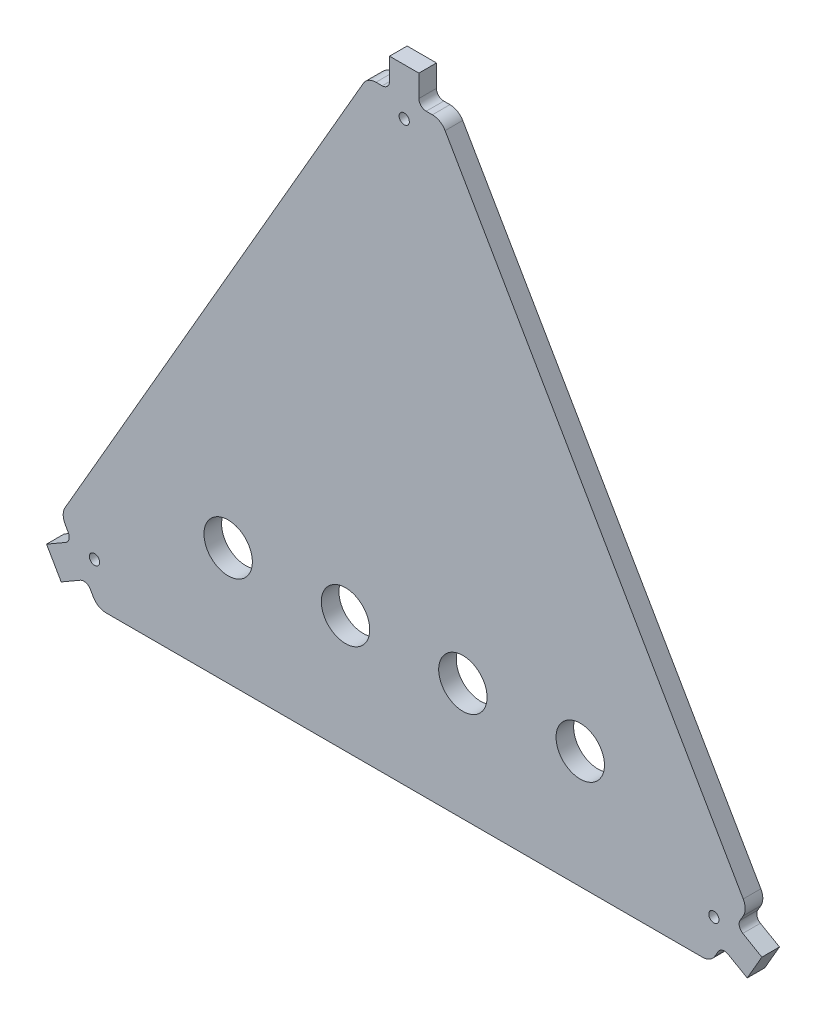
SolidWorks part; units mm, degrees
material "Pine"
ref_plane "Front Plane" through (0, 0, 0) normal (0, 0, 1) x (1, 0, 0)
ref_plane "Top Plane" through (0, 0, 0) normal (0, 1, 0) x (1, 0, 0)
ref_plane "Right Plane" through (0, 0, 0) normal (1, 0, 0) x (0, 0, -1)
sketch "Sketch1" plane through (0, 0, 0) normal (0, 0, 1) x (1, 0, 0)
  line L0 (-209, 0) -> (209, 0)
  line L1 (209, 0) -> (234, 43.3013)
  line L2 (234, 43.3013) -> (25, 405.2999)
  line L3 (25, 405.2999) -> (-25, 405.2999)
  line L4 (0, 405.2999) -> (0, 0) construction
  line L5 (-234, 43.3013) -> (-25, 405.2999)
  line L6 (-209, 0) -> (-234, 43.3013)
  dimension "D1" = 60
  dimension "D2" = 418
  dimension "D3" = 418
  dimension "D4" = 50
  dimension "D5" = 50
extrude "Boss-Extrude1" add sketch "Sketch1" along normal blind 12
sketch "Sketch2" plane through (0, 0, 12) normal (0, 0, 1) x (1, 0, 0)
  line L0 (-221.5, 21.6506) -> (-211.1077, 27.6506) construction
  line L1 (-234, 43.3013) -> (-209, 0) construction
  line L2 (211.1077, 27.6506) -> (221.5, 21.6506) construction
  line L3 (209, 0) -> (234, 43.3013) construction
  line L4 (0, 405.2999) -> (0, 393.2999) construction
  line L5 (25, 405.2999) -> (-25, 405.2999) construction
  circle A0 centre (211.1077, 27.6506) radius 3.5
  circle A1 centre (0, 393.2999) radius 3.5
  circle A2 centre (-211.1077, 27.6506) radius 3.5
  dimension "D1" = 7
  dimension "D2" = 12
extrude "Cut-Extrude1" cut sketch "Sketch2" against normal up to next
fillet "Fillet1" radius 10 6 edges at (-209, 0, 6) (-234, 43.3013, 6) (-25, 405.2999, 6) (25, 405.2999, 6) (209, 0, 6) (234, 43.3013, 6)
sketch "Sketch3" plane through (0, 0, 12) normal (0, 0, 1) x (1, 0, 0)
  line L0 (-40, 80) -> (40, 80) construction
  line L1 (0, 80) -> (0, 0) construction
  line L2 (-120, 80) -> (-40, 80) construction
  line L3 (40, 80) -> (120, 80) construction
  circle A0 centre (-40, 80) radius 16.5
  circle A1 centre (40, 80) radius 16.5
  circle A2 centre (-120, 80) radius 16.5
  circle A3 centre (120, 80) radius 16.5
  dimension "D1" = 33
  dimension "D2" = 33
  dimension "D7" = 33
  dimension "D8" = 33
  dimension "D3" = 80
  dimension "D4" = 80
  dimension "D5" = 80
  dimension "D6" = 80
extrude "Cut-Extrude2" cut sketch "Sketch3" against normal up to next
sketch "Sketch4" plane through (0, 0, 12) normal (0, 0, 1) x (1, 0, 0)
  line L0 (-10, 405.2999) -> (-10, 425.2999)
  line L1 (19.2265, 405.2999) -> (-19.2265, 405.2999) construction
  line L2 (-10, 425.2999) -> (10, 425.2999)
  line L3 (10, 425.2999) -> (10, 405.2999)
  line L4 (0, 425.2999) -> (0, 405.2999) construction
  line L5 (-10, 405.2999) -> (10, 405.2999)
  line L6 (226.5, 30.3109) -> (243.8205, 20.3109)
  line L7 (211.8868, 5) -> (231.1132, 38.3013) construction
  line L8 (243.8205, 20.3109) -> (233.8205, 2.9904)
  line L9 (233.8205, 2.9904) -> (216.5, 12.9904)
  line L10 (216.5, 12.9904) -> (226.5, 30.3109)
  line L11 (221.5, 21.6506) -> (238.8205, 11.6506) construction
  line L12 (-226.5, 30.3109) -> (-243.8205, 20.3109)
  line L13 (-231.1132, 38.3013) -> (-211.8868, 5) construction
  line L14 (-243.8205, 20.3109) -> (-233.8205, 2.9904)
  line L15 (-233.8205, 2.9904) -> (-216.5, 12.9904)
  line L16 (-216.5, 12.9904) -> (-226.5, 30.3109)
  line L17 (-221.5, 21.6506) -> (-238.8205, 11.6506) construction
  dimension "D1" = 20
  dimension "D2" = 20
  dimension "D3" = 20
  dimension "D4" = 20
  dimension "D5" = 20
  dimension "D6" = 20
extrude "Boss-Extrude2" add sketch "Sketch4" against normal blind 12
fillet "Fillet2" radius 5 6 edges at (-10, 405.2999, 6) (10, 405.2999, 6) (226.5, 30.3109, 6) (216.5, 12.9904, 6) (-216.5, 12.9904, 6) (-226.5, 30.3109, 6)
